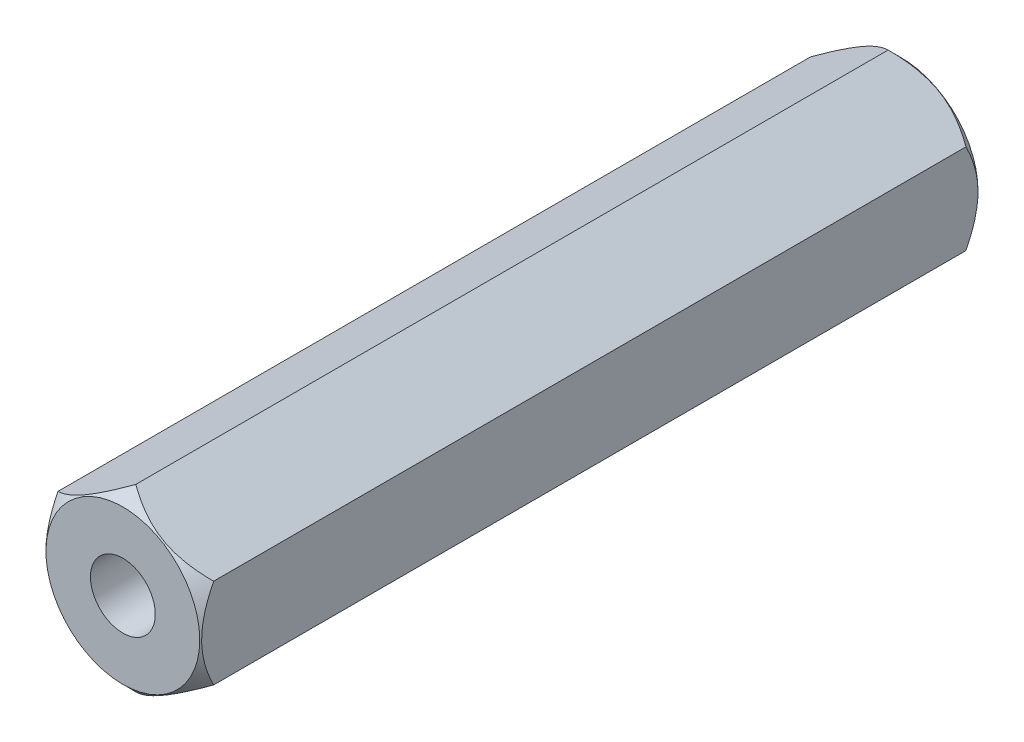
SolidWorks part; units mm, degrees
ref_plane "Plan de face" through (0, 0, 0) normal (0, 0, 1) x (1, 0, 0)
ref_plane "Plan de dessus" through (0, 0, 0) normal (0, 1, 0) x (1, 0, 0)
ref_plane "Plan de droite" through (0, 0, 0) normal (1, 0, 0) x (0, 0, -1)
sketch "Esquisse1" plane through (0, 0, 0) normal (0, 0, 1) x (1, 0, 0)
  line L1 (0, 3.4641) -> (-3, 1.7321)
  line L2 (-3, 1.7321) -> (-3, -1.7321)
  line L3 (-3, -1.7321) -> (0, -3.4641)
  line L4 (0, -3.4641) -> (3, -1.7321)
  line L5 (3, -1.7321) -> (3, 1.7321)
  line L6 (3, 1.7321) -> (0, 3.4641)
  circle A0 centre (0, 0) radius 3 construction
  dimension "D1" = 6
extrude "Boss.-Extru.1" add sketch "Esquisse1" along normal blind 30
sketch "Esquisse2" plane through (0, 0, 0) normal (1, 0, 0) x (0, 0, -1)
  line L0 (-30, 2.9641) -> (-29.5, 3.4641)
  line L1 (-34.5, 7.9641) -> (-29.5, 7.9641)
  line L2 (-34.5, 7.9641) -> (-34.5, 2.9641)
  line L3 (-34.5, 2.9641) -> (-30, 2.9641)
  line L4 (-29.5, 7.9641) -> (-29.5, 3.4641)
  line L5 (0, 2.9641) -> (4.5, 2.9641)
  line L6 (-0.5, 3.4641) -> (-0.5, 7.9641)
  line L7 (-0.5, 7.9641) -> (4.5, 7.9641)
  line L8 (4.5, 2.9641) -> (4.5, 7.9641)
  line L9 (-0.5, 3.4641) -> (0, 2.9641)
  line L10 (-30, 3.4641) -> (0, 3.4641) construction
  line L11 (-30, 1.7321) -> (-30, 3.4641) construction
  line L14 (0, 1.7321) -> (0, 3.4641) construction
  line L15 (-1000, 0) -> (49000, 0) construction
  point P1 (-29.5, 2.9641)
  point P4 (-0.5, 2.9641)
  dimension "D1" = 5
  dimension "D2" = 5
  dimension "D3" = 5
  dimension "D4" = 5
revolve "Enlèvement de matière-Révolution1" cut sketch "Esquisse2" angle 360 about L15
hole_wizard "Trou pour taraudage pour trou taraudé M31" positions "Esquisse4" profile "Esquisse3" hole size "M3" standard "Iso" end condition through all
sketch "Esquisse4" plane through (0, 0, 0) normal (0, 0, -1) x (-1, 0, 0)
  point P0 (0, 0)
sketch "Esquisse3" plane through (0, 0, 0) normal (1, 0, 0) x (0, 1, 0)
  line L0 (0, 0) -> (0, 30)
  line L1 (0, 30) -> (1.25, 30)
  line L2 (1.25, 30) -> (1.25, 0)
  line L5 (1.25, 0) -> (0, 0)
  line L11 (0, -6.35) -> (0, 107.95) construction
  dimension "Diamètre du perçage jusqu'au prochain" = 2.5
  dimension "Profondeur du perçage jusqu'au prochain" = 30
